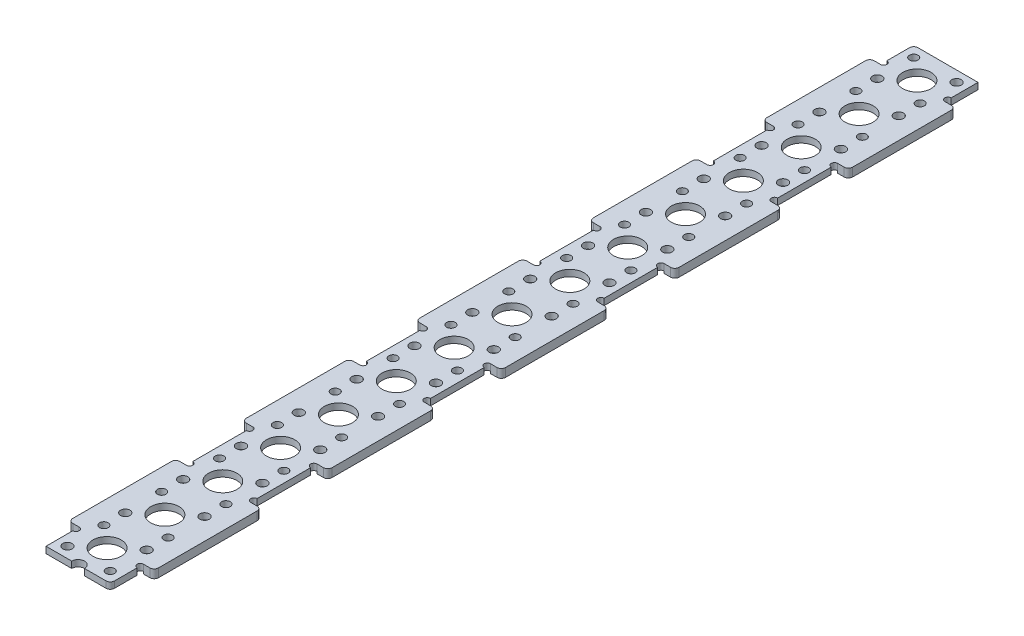
SolidWorks part; units mm, degrees
ref_plane "前视基准面" through (0, 0, 0) normal (0, 0, 1) x (1, 0, 0)
ref_plane "上视基准面" through (0, 0, 0) normal (0, 1, 0) x (1, 0, 0)
ref_plane "右视基准面" through (0, 0, 0) normal (1, 0, 0) x (0, 0, -1)
sketch "草图2" plane through (0, 0, 0) normal (0, 1, 0) x (1, 0, 0)
  line L1 (5, -4.25) -> (-5, -4.25) construction
  line L2 (5, -4.25) -> (5, 4.25) construction
  line L3 (5, 4.25) -> (-5, 4.25) construction
  line L4 (-5, -4.25) -> (-5, 4.25) construction
  line L5 (5, -4.25) -> (-5, 4.25) construction
  line L6 (5, 4.25) -> (-5, -4.25) construction
  circle A0 centre (-5, 4.25) radius 1
  circle A1 centre (-5, -4.25) radius 1.1
  circle A2 centre (5, -4.25) radius 1
  circle A3 centre (5, 4.25) radius 1.1
  point P0 (0, 0)
  dimension "D3" = 2
  dimension "D4" = 2.2
  dimension "D1" = 10
  dimension "D2" = 8.5
sketch "草图4" plane through (0, 0, 0) normal (0, 1, 0) x (1, 0, 0)
  line L0 (0, 0) -> (0, 13.5) construction
  line L1 (-7.5, 195.75) -> (7.5, 195.75)
  line L2 (-7.5, 195.75) -> (-7.5, -6.75)
  line L3 (-7.5, -6.75) -> (7.5, -6.75)
  line L4 (7.5, 195.75) -> (7.5, -6.75)
  line L5 (-7.5, 195.75) -> (7.5, -6.75) construction
  line L6 (-7.5, -6.75) -> (7.5, 195.75) construction
  circle A0 centre (0, 13.5) radius 3.3
  circle A1 centre (0, 0) radius 3.3
  circle A2 centre (0, 27) radius 3.3
  circle A3 centre (0, 40.5) radius 3.3
  circle A4 centre (0, 54) radius 3.3
  circle A5 centre (0, 67.5) radius 3.3
  circle A6 centre (0, 81) radius 3.3
  circle A7 centre (0, 94.5) radius 3.3
  circle A8 centre (0, 108) radius 3.3
  circle A9 centre (0, 121.5) radius 3.3
  circle A10 centre (0, 135) radius 3.3
  circle A11 centre (0, 148.5) radius 3.3
  circle A12 centre (0, 162) radius 3.3
  circle A13 centre (0, 175.5) radius 3.3
  circle A14 centre (0, 189) radius 3.3
  point P0 (0, 94.5)
  dimension "D1" = 6.6
  dimension "D2" = 6.75
  dimension "D6" = 6.75
  dimension "D3" = 15
  dimension "D5" = 13.5
  dimension "D4" = 15
extrude "凸台-拉伸1" add sketch "草图4" along normal mid plane 1.5
extrude "切除-拉伸1" cut sketch "草图2" against normal through all both and the other way through all
pattern_linear "阵列(线性)1" count 15 spacing 13.5 along (0, 0, -1) of "切除-拉伸1"
sketch "草图5" plane through (0, 0.75, 0) normal (0, 1, 0) x (1, 0, 0)
  line L0 (-7.5, -6.75) -> (7.5, -6.75) construction
  circle A0 centre (0, -6.75) radius 1.5
  dimension "D1" = 3
extrude "切除-拉伸2" cut sketch "草图5" against normal through all
sketch "草图6" plane through (0, 0.75, 0) normal (0, 1, 0) x (1, 0, 0)
  line L0 (-7.5, 195.75) -> (-7.5, -6.75) construction
  line L1 (-7.5, 1) -> (-9, 1)
  line L2 (-7.5, 1) -> (-7.5, 26)
  line L3 (-7.5, 26) -> (-9, 26)
  line L4 (-10, 2) -> (-10, 25)
  line L5 (-7.5, -6.75) -> (-1.5, -6.75) construction
  line L6 (0, 27) -> (0, 0) construction
  line L7 (7.5, 26) -> (9, 26)
  line L8 (10, 2) -> (10, 25)
  line L9 (7.5, 1) -> (9, 1)
  line L10 (7.5, 1) -> (7.5, 26)
  arc A5 (9, 26) -> (10, 25) centre (9, 25) cw
  arc A6 (10, 2) -> (9, 1) centre (9, 2) cw
  arc A7 (-9, 1) -> (-10, 2) centre (-9, 2) cw
  arc A8 (-9, 26) -> (-10, 25) centre (-9, 25) ccw
  point P6 (-10, 13.5)
  point P21 (10, 26)
  point P24 (10, 1)
  point P27 (-10, 1)
  point P30 (-10, 26)
  dimension "D3" = 2.5
  dimension "D4" = 1
  dimension "D1" = 25
  dimension "D2" = 20.25
extrude "凸台-拉伸2" add sketch "草图6" against normal blind 2
sketch "草图7" plane through (0, 0.75, 0) normal (0, 1, 0) x (1, 0, 0)
  line L0 (-7.5, 195.75) -> (-7.5, 26) construction
  line L1 (-7.5, 1) -> (-7.5, -6.75) construction
  line L2 (7.5, -6.75) -> (7.5, 1) construction
  line L3 (7.5, 26) -> (7.5, 195.75) construction
  circle A0 centre (-7.5, 26.75) radius 0.75
  circle A1 centre (-7.5, 0.25) radius 0.75
  circle A2 centre (7.5, 0.25) radius 0.75
  circle A3 centre (7.5, 26.75) radius 0.75
  dimension "D1" = 1.5
extrude "切除-拉伸3" cut sketch "草图7" against normal through all
pattern_linear "阵列(线性)2" count 5 spacing 40.5 along (0, 0, -1) of "凸台-拉伸2", "切除-拉伸3"
fillet "圆角1" radius 1 2 edges at (-7.5, 0, -195.75) (7.5, 0, 6.75)
